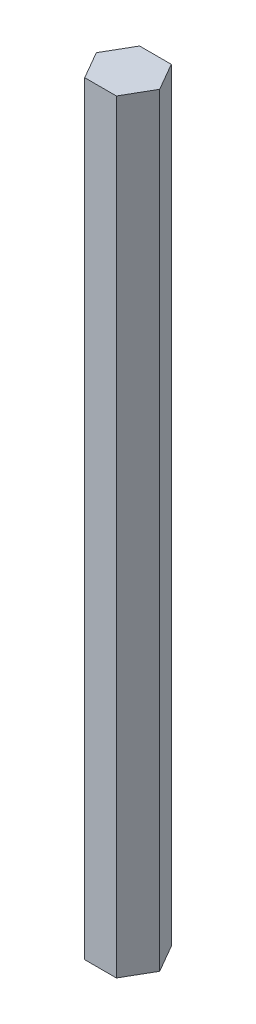
SolidWorks part; units mm, degrees
ref_plane "Front Plane" through (0, 0, 0) normal (0, 0, 1) x (1, 0, 0)
ref_plane "Top Plane" through (0, 0, 0) normal (0, 1, 0) x (1, 0, 0)
ref_plane "Right Plane" through (0, 0, 0) normal (1, 0, 0) x (0, 0, -1)
sketch "Sketch1" plane through (0, 0, 0) normal (0, 1, 0) x (1, 0, 0)
  line L1 (7.9771, 1.5793) -> (3.9771, 8.5075)
  line L2 (3.9771, 8.5075) -> (-4.0229, 8.5075)
  line L3 (-4.0229, 8.5075) -> (-8.0229, 1.5793)
  line L4 (-8.0229, 1.5793) -> (-4.0229, -5.3489)
  line L5 (-4.0229, -5.3489) -> (3.9771, -5.3489)
  line L6 (3.9771, -5.3489) -> (7.9771, 1.5793)
  circle A0 centre (-0.0229, 1.5793) radius 6.9282 construction
  dimension "D1" = 8
extrude "Boss-Extrude1" add sketch "Sketch1" along normal blind 192.89
